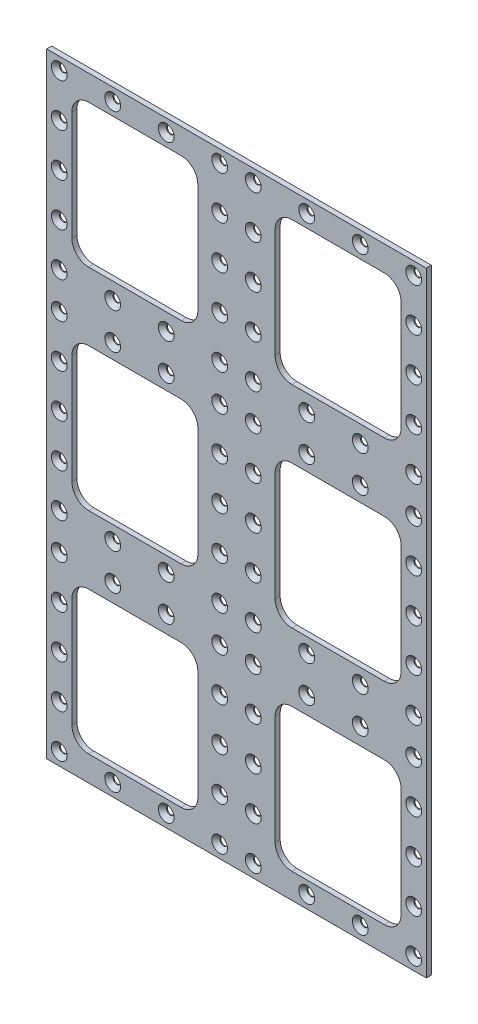
SolidWorks part; units mm, degrees
material "6061-T6 (SS)"
ref_plane "Alzado" through (0, 0, 0) normal (0, 0, 1) x (1, 0, 0)
ref_plane "Planta" through (0, 0, 0) normal (0, 1, 0) x (1, 0, 0)
ref_plane "Vista lateral" through (0, 0, 0) normal (1, 0, 0) x (0, 0, -1)
sketch "Sketch1" plane through (0, 0, 0) normal (0, 0, 1) x (1, 0, 0)
  line L1 (-113, 183) -> (113, 183)
  line L2 (-113, 183) -> (-113, -183)
  line L3 (-113, -183) -> (113, -183)
  line L4 (113, 183) -> (113, -183)
  line L5 (-113, 183) -> (113, -183) construction
  line L6 (-113, -183) -> (113, 183) construction
  point P0 (0, 0)
  dimension "D1" = 366
  dimension "D2" = 226
extrude "Boss-Extrude1" add sketch "Sketch1" along normal blind 3
sketch "Sketch2" plane through (0, 0, 0) normal (0, 0, 1) x (1, 0, 0)
  line L0 (0, 186.1376) -> (0, -191.1438) construction
  line L1 (-164.2926, 0) -> (162.9273, 0) construction
  line L2 (113, 183) -> (-113, 183) construction
  line L3 (-98, 168) -> (-23, 168)
  line L4 (-98, 168) -> (-98, 83)
  line L5 (-98, 83) -> (-23, 83)
  line L6 (-23, 168) -> (-23, 83)
  line L7 (-98, 168) -> (-23, 83) construction
  line L8 (-98, 83) -> (-23, 168) construction
  line L9 (-113, 183) -> (-113, -183) construction
  point P5 (-60.5, 125.5)
  dimension "D1" = 15
  dimension "D2" = 15
  dimension "D3" = 75
  dimension "D4" = 85
extrude "Cut-Extrude4" cut sketch "Sketch2" along normal through all
fillet "Fillet1" radius 10 4 edges at (-23, 83, 1.5) (-23, 168, 1.5) (-98, 83, 1.5) (-98, 168, 1.5)
pattern_linear "LPattern1" count 3 spacing 125.5 along (0, -1, 0) count 2 spacing 121 along (1, 0, 0) of "Cut-Extrude4", "Fillet1"
sketch "Sketch12" plane through (0, 0, 3) normal (0, 0, 1) x (1, 0, 0)
  line L0 (113, 183) -> (-113, 183) construction
  line L1 (-113, 183) -> (-113, -183) construction
  point P0 (-105.5, 175.5)
  dimension "D1" = 7.5
  dimension "D2" = 7.5
hole_wizard "CSK for M4 Flat Head Machine Screw4" positions "Sketch12" profile "Sketch13" countersink size "M4" standard "ANSI Metric" end condition through all
sketch "Sketch13" plane through (-105.5, 175.5, 3) normal (1, 0, 0) x (0, -1, 0)
  line L0 (0, 0) -> (0, 3)
  line L1 (0, 3) -> (2.25, 3)
  line L2 (2.25, 3) -> (2.25, 2.45)
  line L3 (2.25, 2.45) -> (4.7, 0)
  line L5 (4.7, 0) -> (0, 0)
  line L6 (-2.25, 2.45) -> (-4.7, 0) construction
  line L11 (0, -6.35) -> (0, 107.95) construction
  dimension "Thru Hole Dia." = 4.5
  dimension "Thru Hole Depth" = 3
  dimension "Near C'Sink Dia." = 9.4
  dimension "Near C'Sink Angle" = 90
sketch "Sketch14" plane through (0, 0, 3) normal (0, 0, 1) x (1, 0, 0)
  line L0 (0, 183) -> (0, -183) construction
  line L1 (113, 183) -> (-113, 183) construction
  line L2 (-113, -183) -> (113, -183) construction
  line L3 (-113, 62.75) -> (113, 62.75) construction
  line L4 (-113, 183) -> (-113, -183) construction
  line L5 (113, -183) -> (113, 183) construction
  line L6 (-113, -62.75) -> (113, -62.75) construction
  line L7 (-88, 83) -> (-33, 83) construction
  line L8 (-33, 42.5) -> (-88, 42.5) construction
  line L9 (-88, -42.5) -> (-33, -42.5) construction
  line L10 (-33, -83) -> (-88, -83) construction
pattern_linear "LPattern7" count 4 spacing 31.8333 along (1, 0, 0) count 5 spacing 25.6562 along (0, -1, 0) skipping (1, 1), (1, 2), (1, 3), (2, 1), (2, 2), (2, 3) of "CSK for M4 Flat Head Machine Screw4"
pattern_linear "LPattern8" count 3 spacing 124.1875 along (0, -1, 0) of "LPattern7", "CSK for M4 Flat Head Machine Screw4"
mirror "Mirror1" about plane through (0, 0, 0) normal (1, 0, 0) of "LPattern8", "CSK for M4 Flat Head Machine Screw4", "LPattern7"
sketch "Sketch15" [suppressed] plane through (0, 0, 3) normal (0, 0, 1) x (1, 0, 0)
  circle A0 centre (0, 0) radius 10
  dimension "D1" = 20
extrude "Cut-Extrude5" [suppressed] cut sketch "Sketch15" against normal up to next
